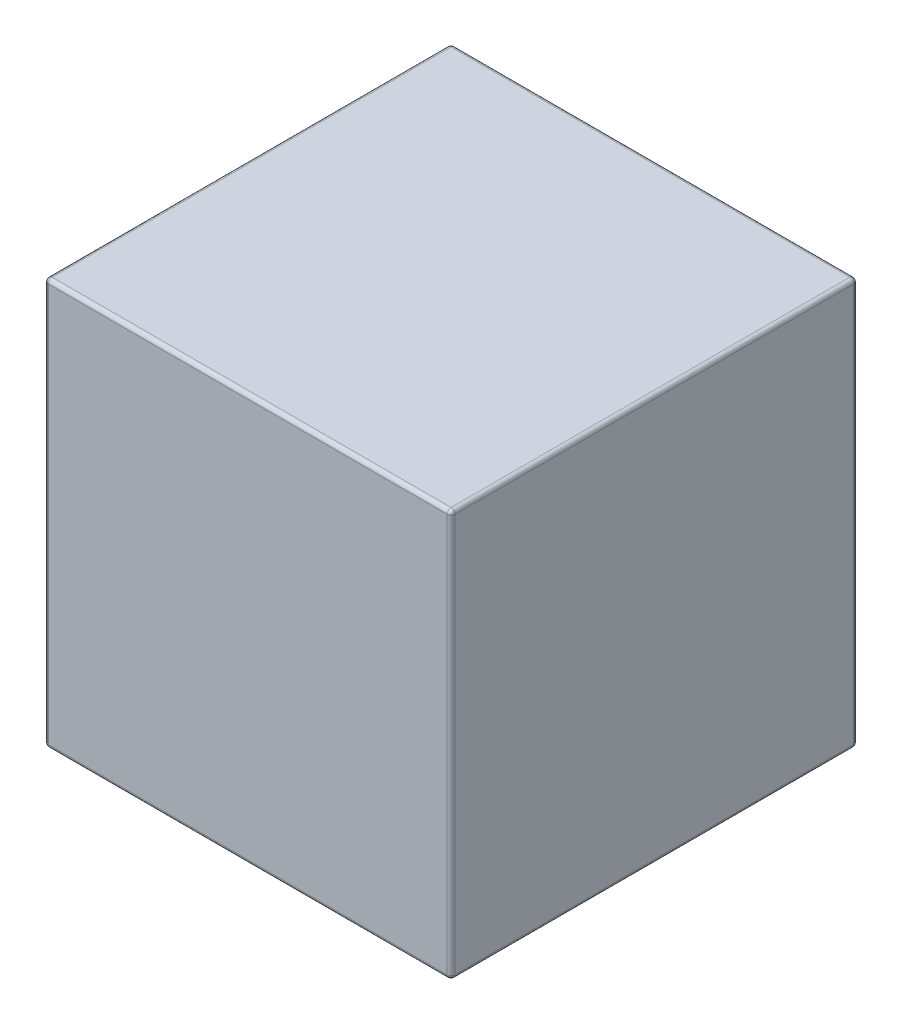
SolidWorks part; units mm, degrees
ref_plane "前视基准面" through (0, 0, 0) normal (0, 0, 1) x (1, 0, 0)
ref_plane "上视基准面" through (0, 0, 0) normal (0, 1, 0) x (1, 0, 0)
ref_plane "右视基准面" through (0, 0, 0) normal (1, 0, 0) x (0, 0, -1)
sketch "草图1" plane through (0, 0, 0) normal (0, 0, 1) x (1, 0, 0)
  line L1 (26, -26) -> (-26, -26)
  line L2 (26, -26) -> (26, 26)
  line L3 (26, 26) -> (-26, 26)
  line L4 (-26, -26) -> (-26, 26)
  line L5 (26, -26) -> (-26, 26) construction
  line L6 (26, 26) -> (-26, -26) construction
  point P0 (0, 0)
  dimension "D1" = 52
  dimension "D2" = 52
extrude "凸台-拉伸1" add sketch "草图1" along normal blind 52
fillet "圆角1" radius 0.5 12 edges at (-26, 26, 26) (0, 26, 52) (-26, 0, 52) (-26, -26, 26) (0, -26, 52) (0, -26, 0) (0, 26, 0) (-26, 0, 0) (26, -26, 26) (26, 0, 52) (26, 26, 26) (26, 0, 0)
